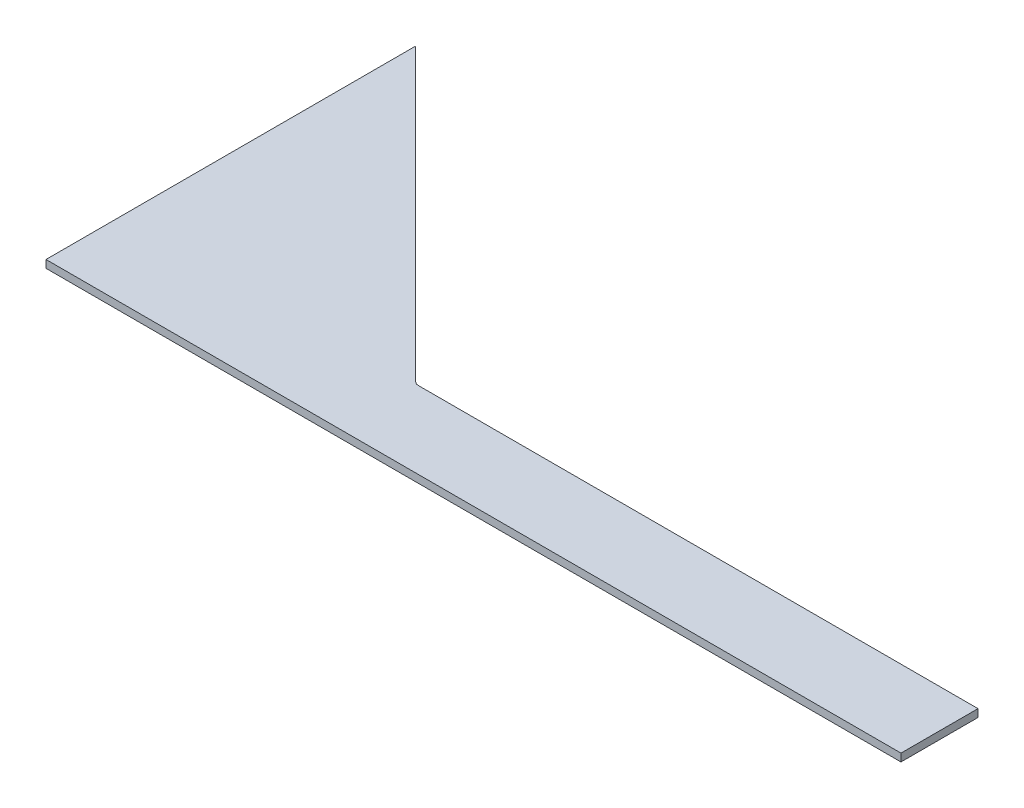
SolidWorks part; units mm, degrees
material "ASTM A36 Steel"
ref_plane "Front Plane" through (0, 0, 0) normal (0, 0, 1) x (1, 0, 0)
ref_plane "Top Plane" through (0, 0, 0) normal (0, 1, 0) x (1, 0, 0)
ref_plane "Right Plane" through (0, 0, 0) normal (1, 0, 0) x (0, 0, -1)
sketch "Sketch1" plane through (0, 0, 0) normal (0, 1, 0) x (1, 0, 0)
  line L0 (0, 0) -> (0, 152.4)
  line L1 (0, 152.4) -> (152.4, 0)
  line L2 (152.4, 0) -> (0, 0)
  line L3 (120.65, 31.75) -> (352.425, 31.75)
  line L4 (352.425, 31.75) -> (352.425, 0)
  line L5 (352.425, 0) -> (152.4, 0)
  arc A0 (119.7201, 32.6799) -> (121.9651, 31.75) centre (121.9651, 34.925) ccw
  dimension "D5" = 3.175
  dimension "D1" = 152.4
  dimension "D2" = 152.4
  dimension "D3" = 352.425
  dimension "D4" = 31.75
extrude "Boss-Extrude1" add sketch "Sketch1" along normal blind 3.175 contours L2 L1 L0 | L5 L4 L3 L1
sketch3d "TAG"
  line L0 (0, 3.175, 0) -> (0, 3.175, -152.4) construction
  line L1 (0, 3.175, 0) -> (0, 0, 0) construction
  line L2 (352.425, 3.175, 0) -> (0, 3.175, 0) construction
  line L3 (0, 3.175, 0) -> (0, 3.175, -152.4)
  line L4 (0, 3.175, 0) -> (0, 0, 0)
  line L5 (352.425, 3.175, 0) -> (0, 3.175, 0)
  dimension "D1" = 3.175
  dimension "D2" = 152.4
  dimension "D3" = 352.425
fillet "Fillet1" radius 2.54 1 edges at (120.65, 1.5875, -31.75)
